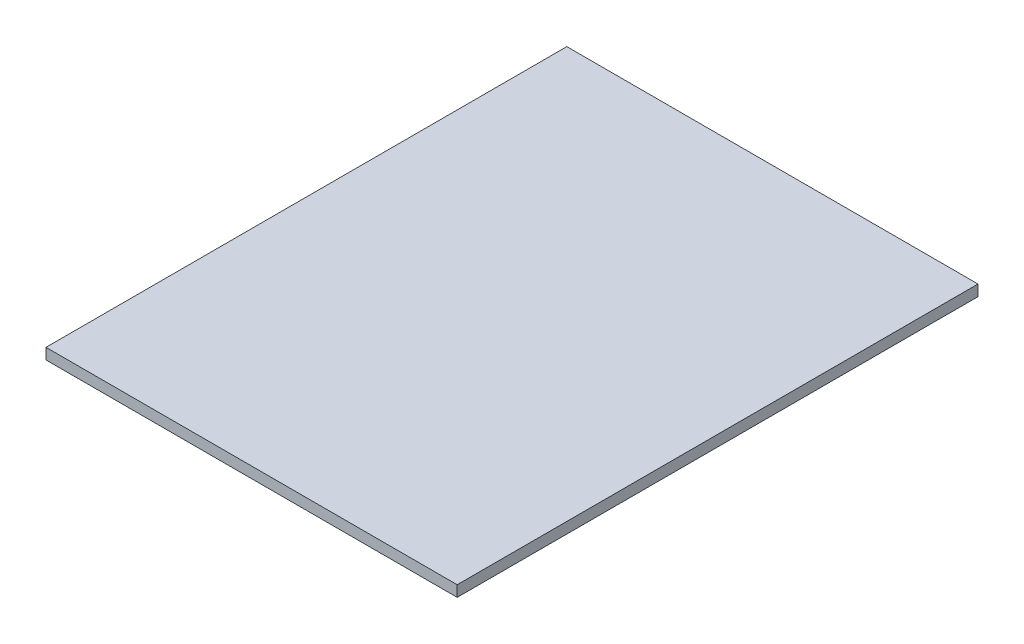
SolidWorks part; units mm, degrees
ref_plane "Front Plane" through (0, 0, 0) normal (0, 0, 1) x (1, 0, 0)
ref_plane "Top Plane" through (0, 0, 0) normal (0, 1, 0) x (1, 0, 0)
ref_plane "Right Plane" through (0, 0, 0) normal (1, 0, 0) x (0, 0, -1)
sketch "Sketch1" plane through (0, 0, 0) normal (0, 1, 0) x (1, 0, 0)
  line L1 (-95.25, -120.65) -> (95.25, -120.65)
  line L2 (-95.25, -120.65) -> (-95.25, 120.65)
  line L3 (-95.25, 120.65) -> (95.25, 120.65)
  line L4 (95.25, -120.65) -> (95.25, 120.65)
  line L5 (-95.25, -120.65) -> (95.25, 120.65) construction
  line L6 (-95.25, 120.65) -> (95.25, -120.65) construction
  point P0 (0, 0)
  dimension "D1" = 190.5
  dimension "D2" = 241.3
extrude "Boss-Extrude1" add sketch "Sketch1" along normal blind 5.08
